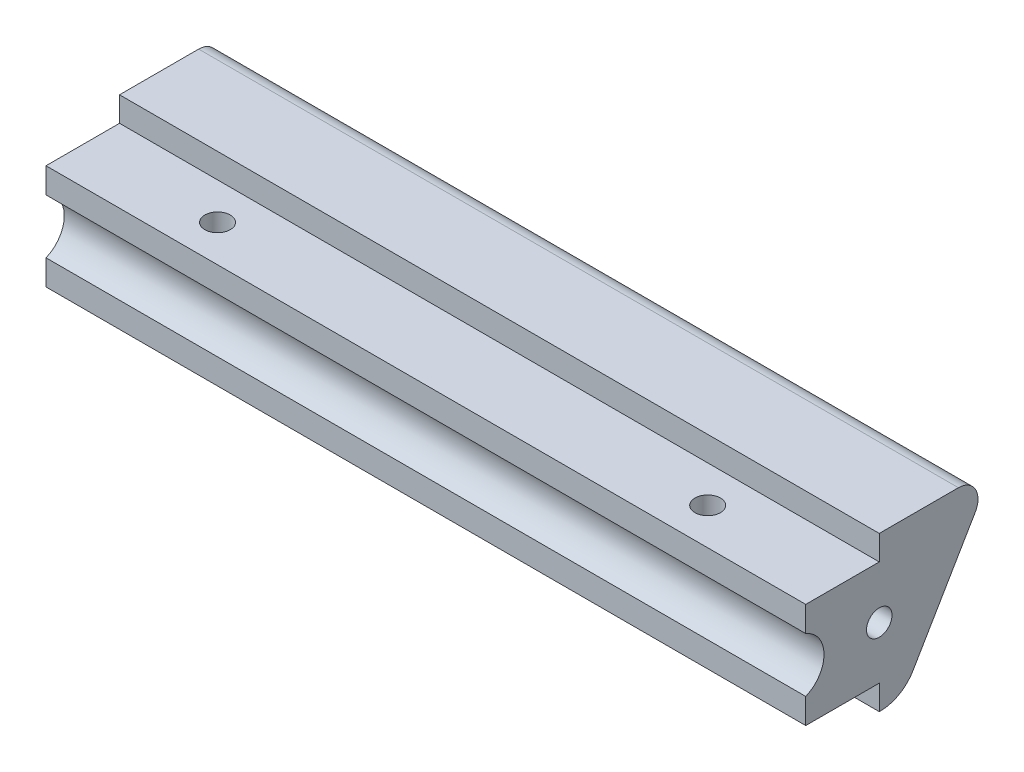
SolidWorks part; units mm, degrees
ref_plane "Front Plane" through (0, 0, 0) normal (0, 0, 1) x (1, 0, 0)
ref_plane "Top Plane" through (0, 0, 0) normal (0, 1, 0) x (1, 0, 0)
ref_plane "Right Plane" through (0, 0, 0) normal (1, 0, 0) x (0, 0, -1)
sketch "Sketch1" plane through (0, 0, 0) normal (1, 0, 0) x (0, 0, -1)
  line L0 (0, 16.7996) -> (0, 3.2004)
  line L1 (0, 20) -> (9.672, 20) construction
  line L2 (0, 20) -> (0, 0) construction
  line L3 (0, 0) -> (9.672, 0) construction
  line L4 (9.672, 20) -> (9.672, 0) construction
  line L5 (0, 20) -> (9.672, 20) construction
  line L6 (0, 20) -> (0, 16.7996) construction
  line L9 (0, 3.2004) -> (9.525, 3.2004)
  line L10 (0, 3.2004) -> (0, 0) construction
  line L11 (0, 0) -> (9.672, 0) construction
  line L14 (24.2156, 20) -> (13.8937, 2.417)
  line L15 (9.672, 0) -> (9.525, 0)
  line L16 (9.525, 3.2004) -> (9.525, 0)
  line L17 (24.2156, 20) -> (9.525, 20)
  line L18 (9.525, 20) -> (9.525, 16.7996)
  line L19 (9.525, 16.7996) -> (0, 16.7996)
  line L20 (39.2831, 45.6667) -> (13.8937, 2.417) construction
  arc A2 (13.8937, 2.417) -> (9.672, 0) centre (9.672, 4.8953) cw
  dimension "D4" = 9.525
  dimension "D1" = 20
  dimension "D3" = 3.2004
extrude "Boss-Extrude1" add sketch "Sketch1" along normal blind 98.425
sketch "Sketch4" plane through (0, 0, 0) normal (-1, 0, 0) x (0, 0, 1)
  line L1 (0, 13.5263) -> (0, 6.4737)
  line L2 (-18.3452, 10) -> (1.4427, 10) construction
  line L3 (0, 3.2004) -> (-9.525, 3.2004) construction
  line L4 (0, 16.7996) -> (0, 3.2004) construction
  line L5 (-13.8937, 2.417) -> (-24.2156, 20) construction
  arc A0 (0, 13.5263) -> (0, 6.4737) centre (1.4427, 10) ccw
  point P3 (0, 10)
  dimension "D1" = 3.81
  dimension "D2" = 1.4427
extrude "Cut-Extrude2" cut sketch "Sketch4" against normal up to surface (98.425 mm away) up to face at (98.425, 9.0951, -9.5781)
sketch "Sketch5" plane through (0, 16.7996, 0) normal (0, 1, 0) x (1, 0, 0)
  line L0 (49.2125, 9.525) -> (49.2125, 0) construction
  line L1 (17.4625, 4.7625) -> (80.9625, 4.7625) construction
  line L2 (98.425, 9.525) -> (0, 9.525) construction
  line L3 (98.425, 0) -> (0, 0) construction
  circle A4 centre (17.4625, 4.7625) radius 1.651
  circle A5 centre (80.9625, 4.7625) radius 1.651
  point P8 (49.2125, 4.7625)
  dimension "D1" = 63.5
  dimension "D2" = 3.302
extrude "Cut-Extrude3" cut sketch "Sketch5" against normal up to surface (13.5992 mm away) up to face at (49.2125, 3.2004, -4.7625)
fillet "Fillet1" radius 2.54 1 edges at (49.2125, 20, -24.2156)
sketch "Sketch6" plane through (98.425, 0, 0) normal (1, 0, 0) x (0, 0, -1)
  line L0 (9.525, 16.7996) -> (9.525, 3.2004) construction
  circle A0 centre (9.525, 10) radius 1.651
  dimension "D1" = 3.302
extrude "Cut-Extrude4" cut sketch "Sketch6" against normal up to surface (98.425 mm away) up to face at (0, 9.8887, -8.9344)
